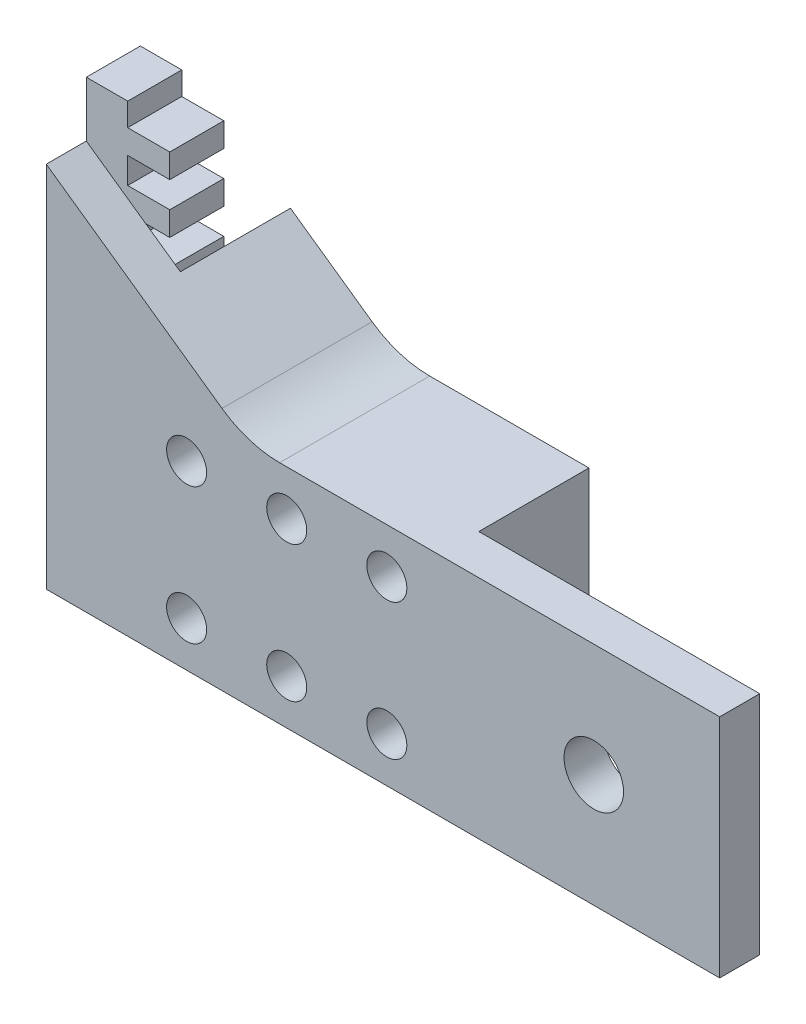
SolidWorks part; units mm, degrees
ref_plane "Front Plane" through (0, 0, 0) normal (0, 0, 1) x (1, 0, 0)
ref_plane "Top Plane" through (0, 0, 0) normal (0, 1, 0) x (1, 0, 0)
ref_plane "Right Plane" through (0, 0, 0) normal (1, 0, 0) x (0, 0, -1)
sketch "Sketch2" plane through (0, 0, 0) normal (0, 0, 1) x (1, 0, 0)
  line L0 (11.9823, 125.1996) -> (11.9823, 121.8976)
  line L3 (17.3163, 121.8976) -> (17.3163, 118.8496)
  line L6 (17.3163, 115.5476) -> (11.9823, 115.5476)
  line L7 (17.3163, 121.8976) -> (11.9823, 121.8976)
  line L8 (17.3163, 128.2476) -> (11.9823, 128.2476)
  line L9 (17.3163, 125.1996) -> (11.9823, 125.1996)
  line L10 (11.9823, 99.7996) -> (11.9823, 96.4976)
  line L11 (17.3163, 102.8476) -> (17.3163, 99.7996)
  line L12 (11.9823, 106.1496) -> (11.9823, 102.8476)
  line L13 (17.3163, 109.1976) -> (17.3163, 106.1496)
  line L14 (17.3163, 118.8496) -> (11.9823, 118.8496)
  line L15 (11.9823, 118.8496) -> (11.9823, 115.5476)
  line L16 (17.3163, 109.1976) -> (11.9823, 109.1976)
  line L17 (11.9823, 112.4996) -> (11.9823, 109.1976)
  line L18 (17.3163, 112.4996) -> (11.9823, 112.4996)
  line L19 (17.3163, 115.5476) -> (17.3163, 112.4996)
  line L20 (17.3163, 102.8476) -> (11.9823, 102.8476)
  line L21 (17.3163, 128.2476) -> (17.3163, 125.1996)
  line L22 (17.3163, 106.1496) -> (11.9823, 106.1496)
  line L23 (17.3163, 134.5976) -> (11.9823, 134.5976)
  line L24 (17.3163, 131.5496) -> (11.9823, 131.5496)
  line L25 (17.3163, 134.5976) -> (17.3163, 131.5496)
  line L26 (17.3163, 99.7996) -> (11.9823, 99.7996)
  line L27 (17.3163, 140.9476) -> (11.9823, 140.9476)
  line L31 (17.3163, 137.8996) -> (11.9823, 137.8996)
  line L32 (11.9823, 96.4976) -> (6.7294, 96.4976)
  line L33 (6.7294, 125.1996) -> (6.7294, 96.4976)
  line L34 (17.3163, 140.9476) -> (17.3163, 137.8996)
  line L35 (17.3163, 147.2976) -> (11.9823, 147.2976)
  line L36 (17.3163, 144.2496) -> (11.9823, 144.2496)
  line L37 (17.3163, 147.2976) -> (17.3163, 144.2496)
  line L39 (11.9823, 128.2476) -> (11.9823, 131.5496)
  line L40 (11.9823, 134.5976) -> (11.9823, 137.8996)
  line L41 (11.9823, 140.9476) -> (11.9823, 144.2496)
  line L42 (6.7294, 125.1996) -> (6.7294, 150.2186)
  line L43 (6.7294, 150.2186) -> (11.9823, 150.2186)
  line L44 (11.9823, 150.2186) -> (11.9823, 147.2976)
  line L52 (17.3163, 96.4976) -> (11.9823, 96.4976) [skipped]
  point P12 (14.6493, 123.5486)
  dimension "D1" = 5
  dimension "D3" = 5
extrude "Boss-Extrude1" add sketch "Sketch2" along normal blind 6.858
sketch "Sketch3" plane through (0, 0, 6.858) normal (0, 0, 1) x (1, 0, 0)
  line L2 (6.7294, 125.1996) -> (6.7294, 96.4976)
  line L3 (6.7294, 96.4976) -> (16.344, 96.4976)
  line L4 (29.0243, 127.514) -> (6.7294, 143.2054)
  line L5 (32.3126, 96.4976) -> (16.344, 96.4976)
  line L6 (32.5718, 110.8486) -> (20.9114, 110.8486) construction
  line L7 (0, 110.8486) -> (76.2, 110.8486) construction
  line L8 (6.7294, 150.2186) -> (6.7294, 96.4976) construction
  line L9 (36.3338, 125.1996) -> (78.2335, 125.1996)
  line L10 (6.7294, 143.2054) -> (6.7294, 125.1996)
  line L11 (32.3126, 96.4976) -> (78.2335, 96.4976)
  line L12 (78.2335, 125.1996) -> (92.1758, 125.1996)
  line L14 (78.2335, 96.4976) -> (92.1758, 96.4976)
  line L15 (92.1758, 125.1996) -> (92.1758, 96.4976)
  circle A0 centre (24.5391, 102.2125) radius 2.54
  circle A1 centre (76.2, 110.8486) radius 3.7744
  circle A2 centre (24.5391, 119.4848) radius 2.54
  circle A3 centre (37.2391, 119.4848) radius 2.54
  circle A4 centre (37.2391, 102.2125) radius 2.54
  circle A5 centre (49.9391, 119.4848) radius 2.54
  circle A6 centre (49.9391, 102.2125) radius 2.54
  arc A7 (29.0243, 127.514) -> (36.3338, 125.1996) centre (36.3338, 137.8996) ccw
  dimension "D1" = 76.2
  dimension "D2" = 3
  dimension "D3" = 12.7
extrude "Boss-Extrude2" add sketch "Sketch3" along normal blind 5.08
sketch "Sketch4" plane through (0, 0, 6.858) normal (0, 0, -1) x (-1, 0, 0)
  line L3 (-29.0243, 127.514) -> (-14.2681, 137.8996) construction
  line L4 (-11.9823, 96.4976) -> (-92.1758, 96.4976) construction
  line L6 (-92.1758, 125.1996) -> (-36.3338, 125.1996) construction
  line L7 (-29.0243, 127.514) -> (-18.664, 134.8057)
  line L8 (-18.664, 96.4976) -> (-56.5368, 96.4976)
  line L10 (-56.5368, 125.1996) -> (-36.3338, 125.1996)
  line L11 (-18.664, 96.4976) -> (-18.664, 134.8057)
  line L12 (-56.5368, 125.1996) -> (-56.5368, 96.4976)
  arc A1 (-36.3338, 125.1996) -> (-29.0243, 127.514) centre (-36.3338, 137.8996) ccw construction
  arc A2 (-36.3338, 125.1996) -> (-29.0243, 127.514) centre (-36.3338, 137.8996) ccw
  circle A3 centre (-49.9391, 102.2125) radius 2.54 construction
  circle A4 centre (-37.2391, 102.2125) radius 2.54 construction
  circle A5 centre (-24.5391, 102.2125) radius 2.54 construction
  circle A6 centre (-24.5391, 119.4848) radius 2.54 construction
  circle A7 centre (-37.2391, 119.4848) radius 2.54 construction
  circle A8 centre (-49.9391, 119.4848) radius 2.54 construction
  circle A9 centre (-49.9391, 102.2125) radius 2.54
  circle A10 centre (-37.2391, 102.2125) radius 2.54
  circle A11 centre (-24.5391, 102.2125) radius 2.54
  circle A12 centre (-24.5391, 119.4848) radius 2.54
  circle A13 centre (-37.2391, 119.4848) radius 2.54
  circle A14 centre (-49.9391, 119.4848) radius 2.54
extrude "Boss-Extrude3" add sketch "Sketch4" along normal blind 13.97
